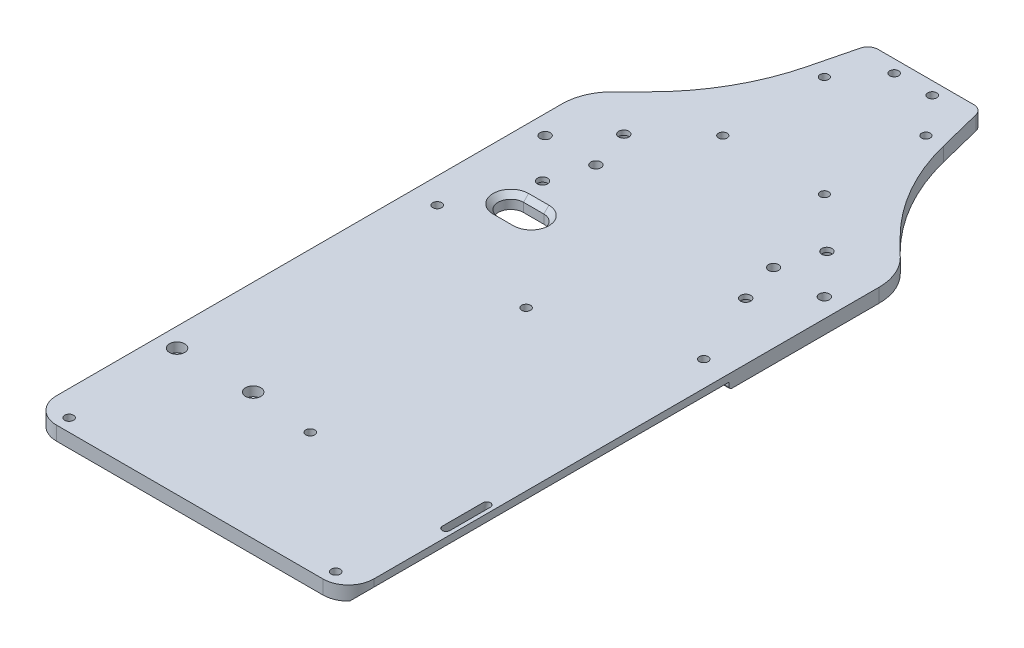
SolidWorks part; units mm, degrees
ref_plane "정면" through (0, 0, 0) normal (0, 0, 1) x (1, 0, 0)
ref_plane "윗면" through (0, 0, 0) normal (0, 1, 0) x (1, 0, 0)
ref_plane "우측면" through (0, 0, 0) normal (1, 0, 0) x (0, 0, -1)
sketch "스케치1" plane through (0, 0, 0) normal (0, 1, 0) x (1, 0, 0)
  line L0 (-857.021, 0) -> (41994.0268, 0) construction
  line L1 (0, -857.021) -> (0, 41994.0268) construction
  line L2 (-72.5, 0) -> (-72.5, -185)
  line L3 (-72.5, 95) -> (72.5, 95) construction
  line L4 (-72.5, 95) -> (-72.5, -195) construction
  line L5 (-72.5, -195) -> (-47.5, -195) construction
  line L6 (72.5, 95) -> (72.5, -195) construction
  line L7 (-62.5, -195) -> (-49.962, -195)
  line L8 (72.5, -185) -> (72.5, 0)
  line L9 (-15.038, -234) -> (15.038, -234)
  line L14 (-19.0011, -232.0486) -> (-45.9989, -196.9514)
  line L15 (-22, 95) -> (22, 95)
  line L16 (-63.6708, 21.2555) -> (-49.4782, 35.3915)
  line L17 (19.0011, -232.0486) -> (45.9989, -196.9514)
  line L18 (857.021, 0) -> (-41994.0268, 0) construction
  line L23 (47.5, -195) -> (72.5, -195) construction
  line L24 (49.962, -195) -> (62.5, -195)
  line L25 (-27, 75) -> (-22, 95)
  line L26 (63.6708, 21.2555) -> (49.4782, 35.3915)
  line L27 (27, 75) -> (22, 95)
  arc A4 (62.5, -195) -> (72.5, -185) centre (62.5, -185) ccw
  arc A5 (-62.5, -195) -> (-72.5, -185) centre (-62.5, -185) cw
  arc A12 (49.962, -195) -> (45.9989, -196.9514) centre (49.962, -200) ccw
  arc A13 (19.0011, -232.0486) -> (15.038, -234) centre (15.038, -229) cw
  arc A14 (-15.038, -234) -> (-19.0011, -232.0486) centre (-15.038, -229) cw
  arc A15 (-49.962, -195) -> (-45.9989, -196.9514) centre (-49.962, -200) cw
  arc A16 (-72.5, 0) -> (-63.6708, 21.2555) centre (-42.5, 0) cw
  arc A17 (-49.4782, 35.3915) -> (-27, 75) centre (-109.4621, 95.6155) ccw
  arc A18 (72.5, 0) -> (63.6708, 21.2555) centre (42.5, 0) ccw
  arc A19 (49.4782, 35.3915) -> (27, 75) centre (109.4621, 95.6155) cw
  point P4 (0, 0)
  point P36 (0, -234)
  point P40 (0, 95)
  point P77 (17.5, -234)
  point P80 (-17.5, -234)
  dimension "D8" = 10
  dimension "D13" = 72.5
  dimension "D14" = 5
  dimension "D17" = 20
  dimension "D15" = 30
  dimension "D16" = 85
  dimension "D1" = 145
  dimension "D2" = 290
  dimension "D3" = 195
  dimension "D9" = 35
  dimension "D10" = 39
  dimension "D11" = 25
  dimension "D12" = 44
  dimension "D18" = 5
extrude "Deck base" add sketch "스케치1" along normal blind 5.5 contours L2 A5 L7 A15 L14 A14 L9 A13 L17 A12 L24 A4 L8 A18 L26 A19 L27 L15 L25 A17 L16 A16
sketch "스케치3" plane through (0, 5.5, 0) normal (0, 1, 0) x (1, 0, 0)
  line L0 (-22, 95) -> (22, 95) construction
  line L1 (0, 0) -> (0, -234) construction
  line L2 (-15.038, -234) -> (15.038, -234) construction
  line L5 (0, -178.2) -> (0, 178.2) construction
  line L6 (0, -200857.021) -> (0, 241994.0268) construction
  circle A0 centre (7.5, 90) radius 1.75
  circle A9 centre (-7.5, 90) radius 1.75
  circle A10 centre (52.5, -45) radius 1.75
  circle A11 centre (52.5, -190) radius 1.75
  circle A14 centre (-52.5, -190) radius 1.75
  circle A15 centre (-52.5, -45) radius 1.75
  dimension "D1" = 3.5
  dimension "D3" = 3.5
  dimension "D8" = 145
  dimension "D9" = 52.5
  dimension "D4" = 3.5
  dimension "D2" = 5
  dimension "D7" = 135
  dimension "D12" = 7.5
extrude "Bolt slot" cut sketch "스케치3" against normal up to next
sketch "스케치14" plane through (0, 5.5, 0) normal (0, 1, 0) x (1, 0, 0)
  circle A0 centre (-52.5, -45) radius 3
  circle A1 centre (52.5, -45) radius 3
  circle A2 centre (-52.5, -45) radius 1.75 construction
  dimension "D1" = 6
  dimension "D4" = 6
extrude "Bolt head" [suppressed] cut sketch "스케치14" against normal blind 2
fillet "필렛1" radius 4 2 edges at (22, 2.75, -95) (-22, 2.75, -95)
sketch "스케치15" plane through (0, 5.5, 0) normal (0, 1, 0) x (1, 0, 0)
  line L0 (72.5, 95) -> (72.5, -195) construction
  line L1 (-72.5, -195) -> (72.5, -195)
  line L2 (-72.5, -195) -> (-72.5, -234)
  line L3 (-72.5, -234) -> (72.5, -234)
  line L4 (72.5, -195) -> (72.5, -234)
  line L5 (-15.038, -234) -> (15.038, -234) construction
extrude "컷-돌출6" cut sketch "스케치15" against normal up to next
sketch "스케치17" plane through (0, 5.5, 0) normal (0, 1, 0) x (1, 0, 0)
  line L0 (-72.5, 95) -> (72.5, 95) construction
  line L1 (-62.5, 95) -> (62.5, 95)
  line L2 (-62.5, 95) -> (-62.5, -195)
  line L3 (-62.5, -195) -> (62.5, -195)
  line L4 (62.5, 95) -> (62.5, -195)
extrude "컷-돌출8" cut sketch "스케치17" against normal blind 10 flip side to cut
fillet "필렛4" radius 10 2 edges at (62.5, 2.75, 195) (-62.5, 2.75, 195)
fillet "필렛5" radius 20 2 edges at (62.5, 2.75, -22.4217) (-62.5, 2.75, -22.4217)
sketch "스케치19" plane through (0, 5.5, 0) normal (0, 1, 0) x (1, 0, 0)
  line L0 (-38.5, -30) -> (-30.5, -30) construction
  line L1 (-38.5, -25) -> (-30.5, -25)
  line L2 (-38.5, -35) -> (-30.5, -35)
  arc A0 (-38.5, -25) -> (-38.5, -35) centre (-38.5, -30) ccw
  arc A1 (-30.5, -35) -> (-30.5, -25) centre (-30.5, -30) ccw
  circle A2 centre (-52.5, -45) radius 1.75 construction
  point P2 (-34.5, -30)
  dimension "D3" = 5
  dimension "D4" = 14
  dimension "D1" = 15
  dimension "D2" = 8
extrude "Motor bolt" cut sketch "스케치19" against normal blind 10
chamfer "모따기1" distance 2 angle 45 4 edges at (-43.5, 5.5, 30) (-34.5, 5.5, 35) (-34.5, 5.5, 25) (-25.5, 5.5, 30)
sketch "스케치22" plane through (0, 5.5, 0) normal (0, 1, 0) x (1, 0, 0)
  line L1 (0, -200857.021) -> (0, 241994.0268) construction
  line L2 (-200857.021, 0) -> (241994.0268, 0) construction
  line L3 (0, 0) -> (0, 95) construction
  line L4 (-22, 95) -> (22, 95) construction
  line L5 (-62.5, 0) -> (62.2387, 0) construction
  line L6 (-62.5, 14.114) -> (-62.5, -185) construction
  circle A1 centre (-55, 0) radius 2
  circle A4 centre (-35, 0) radius 2
  circle A5 centre (-40, 16) radius 2
  circle A6 centre (40, 16) radius 2
  circle A7 centre (35, 0) radius 2
  circle A8 centre (55, 0) radius 2
  circle A9 centre (40, -16) radius 2
  circle A10 centre (-40, -16) radius 2
  dimension "D2" = 4
  dimension "D1" = 4
  dimension "D5" = 4
  dimension "D7" = 16
  dimension "D3" = 55
  dimension "D4" = 20
  dimension "D6" = 40
extrude "컷-돌출9" cut sketch "스케치22" against normal blind 10
sketch "스케치23" plane through (0, 0, 0) normal (0, -1, 0) x (1, 0, 0)
  circle A0 centre (40, 16) radius 2 construction
  circle A1 centre (40, -16) radius 2 construction
  circle A2 centre (-40, -16) radius 2 construction
  circle A3 centre (-40, 16) radius 2 construction
  circle A4 centre (40, 16) radius 2 construction
  circle A5 centre (40, -16) radius 2 construction
  circle A6 centre (-40, -16) radius 2 construction
  circle A7 centre (-40, 16) radius 2 construction
  circle A8 centre (40, 16) radius 3.05
  circle A9 centre (40, -16) radius 3.05
  circle A10 centre (-40, -16) radius 3.05
  circle A11 centre (-40, 16) radius 3.05
  dimension "D1" = 1.05
sketch "Regulator" plane through (0, 5.5, 0) normal (0, 1, 0) x (1, 0, 0)
  line L0 (-62.5, 14.114) -> (-62.5, -185) construction
  line L1 (-62.5, -45) -> (-17.5, -45) construction
  line L2 (-62.5, -45) -> (-62.5, -115) construction
  line L3 (-62.5, -115) -> (-17.5, -115) construction
  line L4 (-17.5, -45) -> (-17.5, -115) construction
  point P11 (-52.5, -45)
  dimension "D1" = 70
  dimension "D2" = 45
sketch "스케치4" plane through (0, 5.5, 0) normal (0, 1, 0) x (1, 0, 0)
  line L0 (-22, 95) -> (22, 95) construction
  line L1 (-20, 75) -> (20, 75) construction
  line L2 (-20, 75) -> (-20, 35) construction
  line L3 (-20, 35) -> (20, 35) construction
  line L4 (20, 75) -> (20, 35) construction
  line L5 (0, -200857.021) -> (0, 241994.0268) construction
  line L6 (0, -3.025) -> (0, 3.025) construction
  circle A0 centre (-20, 75) radius 1.7
  circle A1 centre (-20, 35) radius 1.7
  circle A2 centre (20, 35) radius 1.7
  circle A3 centre (20, 75) radius 1.7
  point P6 (0, 75)
  dimension "D4" = 3.4
  dimension "D5" = 3.4
  dimension "D1" = 40
  dimension "D2" = 40
  dimension "D3" = 20
extrude "Lidar slot" cut sketch "스케치4" against normal up to next
sketch "스케치9" plane through (0, 5.5, 0) normal (0, 1, 0) x (1, 0, 0)
  line L0 (0, -200857.021) -> (0, 241994.0268) construction
  line L1 (-24.5, 80) -> (24.5, 80) construction
  line L2 (-24.5, 80) -> (-24.5, 30) construction
  line L3 (-24.5, 30) -> (-12.5, 30) construction
  line L4 (24.5, 80) -> (24.5, 30) construction
  line L5 (-24.5, 80) -> (24.5, 30) construction
  line L6 (-24.5, 30) -> (24.5, 80) construction
  line L7 (-12.5, 25) -> (12.5, 25) construction
  line L8 (-20, 75) -> (20, 75) construction
  line L9 (12.5, 25) -> (12.5, 30) construction
  line L10 (-12.5, 25) -> (-12.5, 30) construction
  line L11 (12.5, 30) -> (24.5, 30) construction
  point P0 (0, 55)
  point P11 (0, 25)
  dimension "D1" = 49
  dimension "D2" = 50
  dimension "D3" = 5
  dimension "D4" = 25
  dimension "D5" = 5
sketch "스케치6" plane through (0, 5.5, 0) normal (0, 1, 0) x (1, 0, 0)
  line L0 (0, -200857.021) -> (0, 241994.0268) construction
  line L1 (-37, -120) -> (37, -120) construction
  line L2 (-37, -120) -> (-37, -191) construction
  line L3 (-37, -191) -> (37, -191) construction
  line L4 (37, -120) -> (37, -191) construction
  line L6 (0, -3.025) -> (0, 3.025) construction
  line L7 (-12.5, 25) -> (12.5, 25) construction
  circle A0 centre (33.5, -137) radius 1.9
  circle A1 centre (33.5, -176) radius 1.9
  circle A2 centre (-33.5, -176) radius 1.9
  circle A3 centre (-33.5, -137) radius 1.9
  point P4 (0, -120)
  dimension "D3" = 3.8
  dimension "D6" = 3.8
  dimension "D1" = 74
  dimension "D2" = 71
  dimension "D4" = 17
  dimension "D5" = 3.5
  dimension "D7" = 3.5
  dimension "D8" = 15
  dimension "D9" = 145
extrude "Vesc slot" [suppressed] cut sketch "스케치6" against normal up to next
sketch "스케치7" plane through (0, 5.5, 0) normal (0, 1, 0) x (1, 0, 0)
  line L0 (0, -200857.021) -> (0, 241994.0268) construction
  line L1 (-58, -49) -> (58, -49) construction
  line L2 (-58, -49) -> (-58, -161) construction
  line L3 (-58, -161) -> (58, -161) construction
  line L4 (58, -49) -> (58, -161) construction
  line L5 (0, -49) -> (0, -161) construction
  line L7 (12.5, 30) -> (24.5, 30) construction
  circle A6 centre (0, -62.5) radius 1.75
  circle A7 centre (0, -147.5) radius 1.75
  point P4 (0, -49)
  dimension "D9" = 3.5
  dimension "D10" = 3.5
  dimension "D1" = 112
  dimension "D2" = 116
  dimension "D3" = 79
  dimension "D11" = 13.5
  dimension "D12" = 13.5
extrude "Nano slot" cut sketch "스케치7" against normal up to next
sketch "스케치12" plane through (0, 5.5, 0) normal (0, 1, 0) x (1, 0, 0)
  line L1 (-52, -130) -> (-28, -130) construction
  line L2 (-52, -130) -> (-52, -163) construction
  line L3 (-52, -163) -> (-28, -163) construction
  line L4 (-28, -130) -> (-28, -163) construction
  line L5 (-52, -130) -> (-28, -163) construction
  line L6 (-52, -163) -> (-28, -130) construction
  line L7 (-40, -115) -> (-40, -195) construction
  line L10 (-62.5, -115) -> (-17.5, -115) construction
  line L11 (-52.5, -195) -> (52.5, -195) construction
  circle A0 centre (-55, -145) radius 1.75
  circle A1 centre (-25, -145) radius 1.75
  point P0 (-40, -146.5)
  dimension "D3" = 3.5
  dimension "D4" = 3.5
  dimension "D1" = 24
  dimension "D2" = 33
  dimension "D5" = 15
  dimension "D6" = 15
  dimension "D7" = 15
  dimension "D8" = 15
extrude "컷-돌출3" cut sketch "스케치12" against normal up to next
sketch "스케치13" plane through (0, 5.5, 0) normal (0, 1, 0) x (1, 0, 0)
  circle A0 centre (-55, -145) radius 3
  circle A1 centre (-25, -145) radius 3
  dimension "D1" = 6
  dimension "D2" = 6
extrude "컷-돌출4" cut sketch "스케치13" against normal blind 3.7
extrude "컷-돌출10" cut sketch "스케치23" against normal blind 3.7
ref_plane "평면1" through (28.5, -28.5, 0) normal (0.7071, -0.7071, 0) x (0, 0, -1)
sketch "스케치24" plane through (28.5, -28.5, 0) normal (0.7071, -0.7071, 0) x (0, 0, -1)
  line L0 (-195, -37.1231) -> (-195, 37.1231) construction
  line L1 (-195, 48.0833) -> (-45, 48.0833)
  line L2 (-195, 48.0833) -> (-195, 38.0833)
  line L3 (-195, 38.0833) -> (-45, 38.0833)
  line L4 (-45, 48.0833) -> (-45, 38.0833)
  line L5 (-185, 48.0833) -> (14.114, 48.0833) construction
  ellipse E2 centre (-45, 37.1231) end of major axis (-43.25, 37.1231) minor radius 1.2374 construction
  point P6 (-45, 37.1231)
  dimension "D1" = 10
ref_plane "평면2" through (29.9142, -29.9142, 0) normal (0.7071, -0.7071, 0) x (0, 0, -1)
sketch "스케치25" plane through (29.9142, -29.9142, 0) normal (0.7071, -0.7071, 0) x (0, 0, -1)
  line L4 (-45, 48.0833) -> (-195, 48.0833)
  line L5 (-45, 38.0833) -> (-45, 48.0833)
  line L6 (-195, 38.0833) -> (-45, 38.0833)
  line L7 (-195, 48.0833) -> (-195, 38.0833)
  line L8 (-45, 48.0833) -> (-195, 48.0833)
  line L9 (-45, 38.0833) -> (-45, 48.0833)
  line L10 (-195, 38.0833) -> (-45, 38.0833)
  line L11 (-195, 48.0833) -> (-195, 38.0833)
  dimension "D1" = 0
extrude "컷-돌출12" cut sketch "스케치25" along normal up to next
fillet "필렛6" radius 1 1 edges at (61.1642, 0, 45)
sketch "스케치26" plane through (0, 0, 0) normal (0, -1, 0) x (1, 0, 0)
  line L0 (-52.5, 195) -> (52.5, 195) construction
  line L1 (56.8284, 153.5) -> (59.8284, 153.5) construction
  line L2 (56.8284, 153.5) -> (56.8284, 137.5)
  line L3 (56.8284, 137.5) -> (59.8284, 137.5) construction
  line L4 (59.8284, 153.5) -> (59.8284, 137.5)
  line L6 (59.8284, 191.804) -> (59.8284, 44) construction
  arc A0 (56.8284, 153.5) -> (59.8284, 153.5) centre (58.3284, 153.5) cw
  arc A1 (56.8284, 137.5) -> (59.8284, 137.5) centre (58.3284, 137.5) ccw
  dimension "D1" = 3
  dimension "D2" = 16
  dimension "D3" = 41.5
sketch "스케치27" plane through (0, 5.5, 0) normal (0, 1, 0) x (1, 0, 0)
  line L0 (56.8284, -137.5) -> (59.8284, -137.5) construction
  line L2 (58, -137.5) -> (58, -153.5)
  line L4 (61, -137.5) -> (61, -153.5)
  line L5 (58, -137.5) -> (61, -137.5) construction
  line L6 (58, -153.5) -> (61, -153.5) construction
  line L7 (62.5, -195) -> (62.5, -45) construction
  line L8 (56.8284, -153.5) -> (59.8284, -153.5) construction
  arc A0 (58, -153.5) -> (61, -153.5) centre (59.5, -153.5) ccw
  arc A1 (58, -137.5) -> (61, -137.5) centre (59.5, -137.5) cw
  dimension "D3" = 1.5
  dimension "D4" = 1.5
  dimension "D1" = 3
  dimension "D2" = 1.5
loft "컷-로프트2" cut profiles "스케치26", "스케치27"
